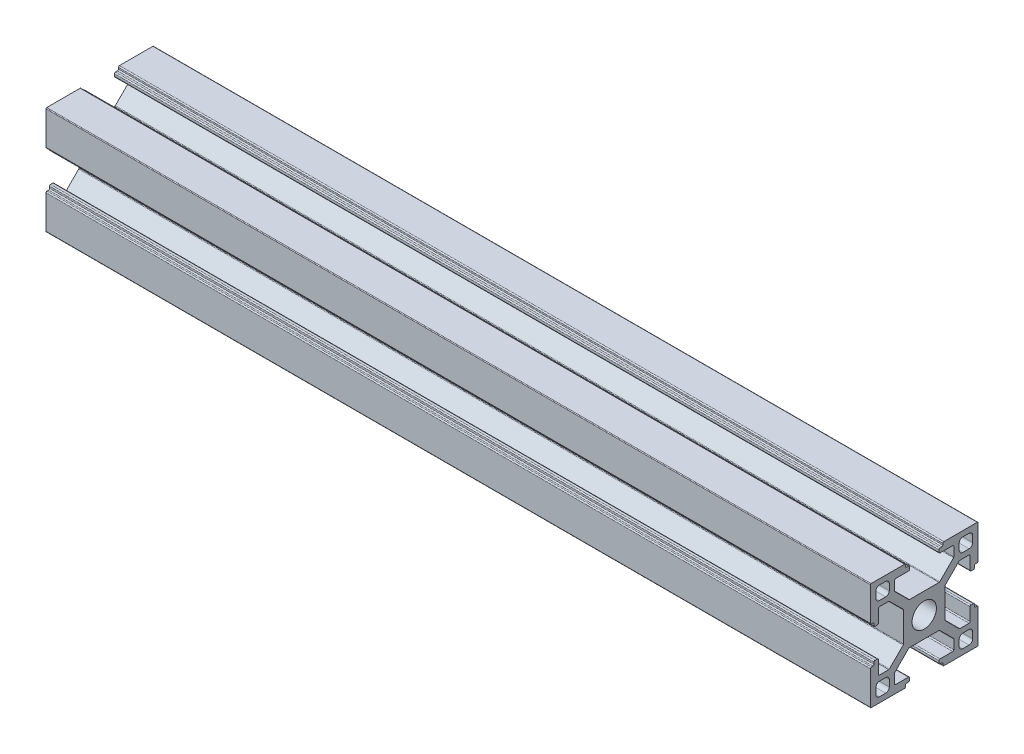
SolidWorks part; units mm, degrees
ref_plane "前视基准面" through (0, 0, 0) normal (0, 0, 1) x (1, 0, 0)
ref_plane "上视基准面" through (0, 0, 0) normal (0, 1, 0) x (1, 0, 0)
ref_plane "右视基准面" through (0, 0, 0) normal (1, 0, 0) x (0, 0, -1)
sketch "草图1" plane through (0, 0, 0) normal (0, 0, 1) x (1, 0, 0)
  line L0 (0, 0) -> (230, 0)
  dimension "D1" = 230
other "3030a 默认<按加工>(1)"
ref_plane "基准面1" through (0, 0, 0) normal (1, 0, 0) x (0, 1, 0)
sketch "草图11" plane through (0, 0, 0) normal (1, 0, 0) x (0, 1, 0)
  line L82 (0, 5.8) -> (-4.1201, 5.8)
  line L83 (-4.3322, 5.8879) -> (-8.1621, 9.7178)
  line L84 (-8.25, 9.9299) -> (-8.25, 12.5)
  line L85 (-7.95, 12.8) -> (-4.4, 12.8)
  line L86 (-4.1, 13.1) -> (-4.1, 13.7)
  line L87 (-4.4, 14) -> (-4.9, 14)
  line L88 (-5.2, 14.3) -> (-5.2, 14.7)
  line L89 (-5.5, 15) -> (-14.8, 15)
  line L90 (-15, 14.8) -> (-15, 5.5)
  line L91 (-14.7, 5.2) -> (-14.3, 5.2)
  line L92 (-14, 4.9) -> (-14, 4.4)
  line L93 (-13.7, 4.1) -> (-13.1, 4.1)
  line L94 (-12.8, 4.4) -> (-12.8, 7.95)
  line L95 (-12.5, 8.25) -> (-9.9299, 8.25)
  line L96 (-9.7178, 8.1621) -> (-5.8879, 4.3322)
  line L97 (-5.8, 4.1201) -> (-5.8, 0)
  line L98 (-5.8, 0) -> (-5.8, -4.1201)
  line L99 (-5.8879, -4.3322) -> (-9.7178, -8.1621)
  line L100 (-9.9299, -8.25) -> (-12.5, -8.25)
  line L101 (-12.8, -7.95) -> (-12.8, -4.4)
  line L102 (-13.1, -4.1) -> (-13.7, -4.1)
  line L103 (-14, -4.4) -> (-14, -4.9)
  line L104 (-14.3, -5.2) -> (-14.7, -5.2)
  line L105 (-15, -5.5) -> (-15, -14.8)
  line L106 (-14.8, -15) -> (-5.5, -15)
  line L107 (-5.2, -14.7) -> (-5.2, -14.3)
  line L108 (-4.9, -14) -> (-4.4, -14)
  line L109 (-4.1, -13.7) -> (-4.1, -13.1)
  line L110 (-4.4, -12.8) -> (-7.95, -12.8)
  line L111 (-8.25, -12.5) -> (-8.25, -9.9299)
  line L112 (-8.1621, -9.7178) -> (-4.3322, -5.8879)
  line L113 (-4.1201, -5.8) -> (0, -5.8)
  line L114 (0, -5.8) -> (4.1201, -5.8)
  line L115 (4.3322, -5.8879) -> (8.1621, -9.7178)
  line L116 (8.25, -9.9299) -> (8.25, -12.5)
  line L117 (7.95, -12.8) -> (4.4, -12.8)
  line L118 (4.1, -13.1) -> (4.1, -13.7)
  line L119 (4.4, -14) -> (4.9, -14)
  line L120 (5.2, -14.3) -> (5.2, -14.7)
  line L121 (5.5, -15) -> (14.8, -15)
  line L122 (15, -14.8) -> (15, -5.5)
  line L123 (14.7, -5.2) -> (14.3, -5.2)
  line L124 (14, -4.9) -> (14, -4.4)
  line L125 (13.7, -4.1) -> (13.1, -4.1)
  line L126 (12.8, -4.4) -> (12.8, -7.95)
  line L127 (12.5, -8.25) -> (9.9299, -8.25)
  line L128 (9.7178, -8.1621) -> (5.8879, -4.3322)
  line L129 (5.8, -4.1201) -> (5.8, 0)
  line L130 (5.8, 0) -> (5.8, 4.1201)
  line L131 (5.8879, 4.3322) -> (9.8056, 8.25)
  line L132 (9.8056, 8.25) -> (12.5, 8.25)
  line L133 (12.8, 7.95) -> (12.8, 4.4)
  line L134 (13.1, 4.1) -> (13.7, 4.1)
  line L135 (14, 4.4) -> (14, 4.9)
  line L136 (14.3, 5.2) -> (14.7, 5.2)
  line L137 (15, 5.5) -> (15, 14.8)
  line L138 (14.8, 15) -> (5.5, 15)
  line L139 (5.2, 14.7) -> (5.2, 14.3)
  line L140 (4.9, 14) -> (4.4, 14)
  line L141 (4.1, 13.7) -> (4.1, 13.1)
  line L142 (4.4, 12.8) -> (7.95, 12.8)
  line L143 (8.25, 12.5) -> (8.25, 9.9299)
  line L144 (8.1621, 9.7178) -> (4.3322, 5.8879)
  line L145 (4.1201, 5.8) -> (0, 5.8)
  line L146 (-10.75, -13.5) -> (-12.5, -13.5)
  line L147 (-13.5, -12.5) -> (-13.5, -10.75)
  line L148 (-12.5, -9.75) -> (-10.75, -9.75)
  line L149 (-9.75, -10.75) -> (-9.75, -12.5)
  line L150 (10.75, -13.5) -> (12.5, -13.5)
  line L151 (13.5, -12.5) -> (13.5, -10.75)
  line L152 (12.5, -9.75) -> (10.75, -9.75)
  line L153 (9.75, -10.75) -> (9.75, -12.5)
  line L154 (-10.75, 13.5) -> (-12.5, 13.5)
  line L155 (-13.5, 12.5) -> (-13.5, 10.75)
  line L156 (-12.5, 9.75) -> (-10.75, 9.75)
  line L157 (-9.75, 10.75) -> (-9.75, 12.5)
  line L158 (10.75, 13.5) -> (12.5, 13.5)
  line L159 (13.5, 12.5) -> (13.5, 10.75)
  line L160 (12.5, 9.75) -> (10.75, 9.75)
  line L161 (9.75, 10.75) -> (9.75, 12.5)
  circle A76 centre (0, 0) radius 3.4
  arc A77 (-4.3322, 5.8879) -> (-4.1201, 5.8) centre (-4.1201, 6.1) ccw
  arc A78 (-8.25, 9.9299) -> (-8.1621, 9.7178) centre (-7.95, 9.9299) ccw
  arc A79 (-7.95, 12.8) -> (-8.25, 12.5) centre (-7.95, 12.5) ccw
  arc A80 (-4.4, 12.8) -> (-4.1, 13.1) centre (-4.4, 13.1) ccw
  arc A81 (-4.1, 13.7) -> (-4.4, 14) centre (-4.4, 13.7) ccw
  arc A82 (-5.2, 14.3) -> (-4.9, 14) centre (-4.9, 14.3) ccw
  arc A83 (-5.2, 14.7) -> (-5.5, 15) centre (-5.5, 14.7) ccw
  arc A84 (-14.8, 15) -> (-15, 14.8) centre (-14.8, 14.8) ccw
  arc A85 (-15, 5.5) -> (-14.7, 5.2) centre (-14.7, 5.5) ccw
  arc A86 (-14, 4.9) -> (-14.3, 5.2) centre (-14.3, 4.9) ccw
  arc A87 (-14, 4.4) -> (-13.7, 4.1) centre (-13.7, 4.4) ccw
  arc A88 (-13.1, 4.1) -> (-12.8, 4.4) centre (-13.1, 4.4) ccw
  arc A89 (-12.5, 8.25) -> (-12.8, 7.95) centre (-12.5, 7.95) ccw
  arc A90 (-9.7178, 8.1621) -> (-9.9299, 8.25) centre (-9.9299, 7.95) ccw
  arc A91 (-5.8, 4.1201) -> (-5.8879, 4.3322) centre (-6.1, 4.1201) ccw
  arc A92 (-5.8879, -4.3322) -> (-5.8, -4.1201) centre (-6.1, -4.1201) ccw
  arc A93 (-9.9299, -8.25) -> (-9.7178, -8.1621) centre (-9.9299, -7.95) ccw
  arc A94 (-12.8, -7.95) -> (-12.5, -8.25) centre (-12.5, -7.95) ccw
  arc A95 (-12.8, -4.4) -> (-13.1, -4.1) centre (-13.1, -4.4) ccw
  arc A96 (-13.7, -4.1) -> (-14, -4.4) centre (-13.7, -4.4) ccw
  arc A97 (-14.3, -5.2) -> (-14, -4.9) centre (-14.3, -4.9) ccw
  arc A98 (-14.7, -5.2) -> (-15, -5.5) centre (-14.7, -5.5) ccw
  arc A99 (-15, -14.8) -> (-14.8, -15) centre (-14.8, -14.8) ccw
  arc A100 (-5.5, -15) -> (-5.2, -14.7) centre (-5.5, -14.7) ccw
  arc A101 (-4.9, -14) -> (-5.2, -14.3) centre (-4.9, -14.3) ccw
  arc A102 (-4.4, -14) -> (-4.1, -13.7) centre (-4.4, -13.7) ccw
  arc A103 (-4.1, -13.1) -> (-4.4, -12.8) centre (-4.4, -13.1) ccw
  arc A104 (-8.25, -12.5) -> (-7.95, -12.8) centre (-7.95, -12.5) ccw
  arc A105 (-8.1621, -9.7178) -> (-8.25, -9.9299) centre (-7.95, -9.9299) ccw
  arc A106 (-4.1201, -5.8) -> (-4.3322, -5.8879) centre (-4.1201, -6.1) ccw
  arc A107 (4.3322, -5.8879) -> (4.1201, -5.8) centre (4.1201, -6.1) ccw
  arc A108 (8.25, -9.9299) -> (8.1621, -9.7178) centre (7.95, -9.9299) ccw
  arc A109 (7.95, -12.8) -> (8.25, -12.5) centre (7.95, -12.5) ccw
  arc A110 (4.4, -12.8) -> (4.1, -13.1) centre (4.4, -13.1) ccw
  arc A111 (4.1, -13.7) -> (4.4, -14) centre (4.4, -13.7) ccw
  arc A112 (5.2, -14.3) -> (4.9, -14) centre (4.9, -14.3) ccw
  arc A113 (5.2, -14.7) -> (5.5, -15) centre (5.5, -14.7) ccw
  arc A114 (14.8, -15) -> (15, -14.8) centre (14.8, -14.8) ccw
  arc A115 (15, -5.5) -> (14.7, -5.2) centre (14.7, -5.5) ccw
  arc A116 (14, -4.9) -> (14.3, -5.2) centre (14.3, -4.9) ccw
  arc A117 (14, -4.4) -> (13.7, -4.1) centre (13.7, -4.4) ccw
  arc A118 (13.1, -4.1) -> (12.8, -4.4) centre (13.1, -4.4) ccw
  arc A119 (12.5, -8.25) -> (12.8, -7.95) centre (12.5, -7.95) ccw
  arc A120 (9.7178, -8.1621) -> (9.9299, -8.25) centre (9.9299, -7.95) ccw
  arc A121 (5.8, -4.1201) -> (5.8879, -4.3322) centre (6.1, -4.1201) ccw
  arc A122 (5.8879, 4.3322) -> (5.8, 4.1201) centre (6.1, 4.1201) ccw
  arc A123 (12.8, 7.95) -> (12.5, 8.25) centre (12.5, 7.95) ccw
  arc A124 (12.8, 4.4) -> (13.1, 4.1) centre (13.1, 4.4) ccw
  arc A125 (13.7, 4.1) -> (14, 4.4) centre (13.7, 4.4) ccw
  arc A126 (14.3, 5.2) -> (14, 4.9) centre (14.3, 4.9) ccw
  arc A127 (14.7, 5.2) -> (15, 5.5) centre (14.7, 5.5) ccw
  arc A128 (15, 14.8) -> (14.8, 15) centre (14.8, 14.8) ccw
  arc A129 (5.5, 15) -> (5.2, 14.7) centre (5.5, 14.7) ccw
  arc A130 (4.9, 14) -> (5.2, 14.3) centre (4.9, 14.3) ccw
  arc A131 (4.4, 14) -> (4.1, 13.7) centre (4.4, 13.7) ccw
  arc A132 (4.1, 13.1) -> (4.4, 12.8) centre (4.4, 13.1) ccw
  arc A133 (8.25, 12.5) -> (7.95, 12.8) centre (7.95, 12.5) ccw
  arc A134 (8.1621, 9.7178) -> (8.25, 9.9299) centre (7.95, 9.9299) ccw
  arc A135 (4.1201, 5.8) -> (4.3322, 5.8879) centre (4.1201, 6.1) ccw
  arc A136 (-10.75, -13.5) -> (-9.75, -12.5) centre (-10.75, -12.5) ccw
  arc A137 (-13.5, -12.5) -> (-12.5, -13.5) centre (-12.5, -12.5) ccw
  arc A138 (-12.5, -9.75) -> (-13.5, -10.75) centre (-12.5, -10.75) ccw
  arc A139 (-9.75, -10.75) -> (-10.75, -9.75) centre (-10.75, -10.75) ccw
  arc A140 (9.75, -12.5) -> (10.75, -13.5) centre (10.75, -12.5) ccw
  arc A141 (12.5, -13.5) -> (13.5, -12.5) centre (12.5, -12.5) ccw
  arc A142 (13.5, -10.75) -> (12.5, -9.75) centre (12.5, -10.75) ccw
  arc A143 (10.75, -9.75) -> (9.75, -10.75) centre (10.75, -10.75) ccw
  arc A144 (-9.75, 12.5) -> (-10.75, 13.5) centre (-10.75, 12.5) ccw
  arc A145 (-12.5, 13.5) -> (-13.5, 12.5) centre (-12.5, 12.5) ccw
  arc A146 (-13.5, 10.75) -> (-12.5, 9.75) centre (-12.5, 10.75) ccw
  arc A147 (-10.75, 9.75) -> (-9.75, 10.75) centre (-10.75, 10.75) ccw
  arc A148 (10.75, 13.5) -> (9.75, 12.5) centre (10.75, 12.5) ccw
  arc A149 (13.5, 12.5) -> (12.5, 13.5) centre (12.5, 12.5) ccw
  arc A150 (12.5, 9.75) -> (13.5, 10.75) centre (12.5, 10.75) ccw
  arc A151 (9.75, 10.75) -> (10.75, 9.75) centre (10.75, 10.75) ccw
  point P0 (0, 0)
